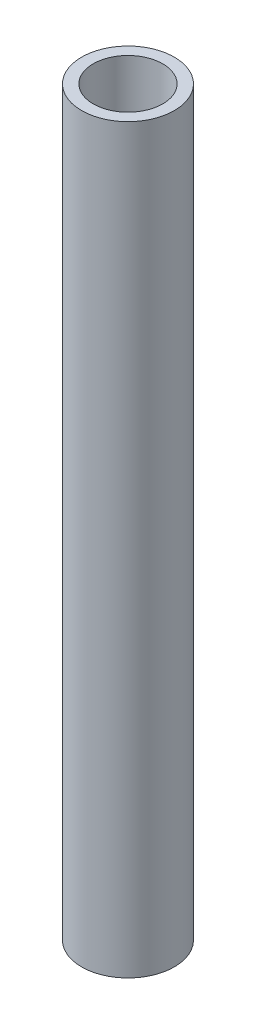
SolidWorks part; units mm, degrees
ref_plane "Front Plane" through (0, 0, 0) normal (0, 0, 1) x (1, 0, 0)
ref_plane "Top Plane" through (0, 0, 0) normal (0, 1, 0) x (1, 0, 0)
ref_plane "Right Plane" through (0, 0, 0) normal (1, 0, 0) x (0, 0, -1)
sketch "Sketch1" plane through (0, 0, 0) normal (0, 1, 0) x (1, 0, 0)
  circle A0 centre (0, 0) radius 1
  circle A1 centre (0, 0) radius 0.75
  dimension "D1" = 1.5
extrude "Boss-Extrude1" add sketch "Sketch1" along normal blind 16
